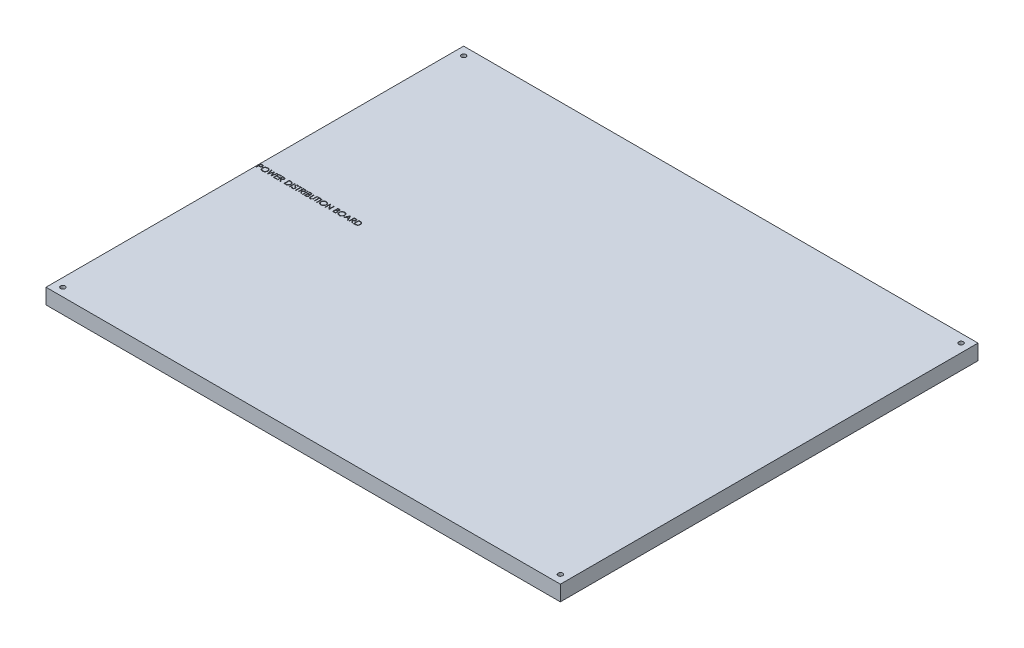
SolidWorks part; units mm, degrees
ref_plane "Front Plane" through (0, 0, 0) normal (0, 0, 1) x (1, 0, 0)
ref_plane "Top Plane" through (0, 0, 0) normal (0, 1, 0) x (1, 0, 0)
ref_plane "Right Plane" through (0, 0, 0) normal (1, 0, 0) x (0, 0, -1)
sketch "Sketch1" plane through (0, 0, 0) normal (0, 1, 0) x (1, 0, 0)
  line L1 (0, 0) -> (335, 0)
  line L2 (0, 0) -> (0, 272)
  line L3 (0, 272) -> (335, 272)
  line L4 (335, 0) -> (335, 272)
  circle A0 centre (5.5, 5.5) radius 1.5
  circle A1 centre (5.5, 266.5) radius 1.5
  circle A2 centre (329.5, 266.5) radius 1.5
  circle A3 centre (329.5, 5.5) radius 1.5
  dimension "D2" = 3
  dimension "D3" = 3
  dimension "D4" = 3
  dimension "D5" = 3
  dimension "D1" = 272
  dimension "D6" = 5.5
  dimension "D7" = 5.5
  dimension "D8" = 5.5
  dimension "D9" = 5.5
  dimension "D10" = 5.5
  dimension "D11" = 5.5
  dimension "D12" = 5.5
  dimension "D13" = 5.5
  dimension "D14" = 335
extrude "Boss-Extrude1" add sketch "Sketch1" along normal blind 10
sketch "Sketch2" plane through (0, 10, 0) normal (0, 1, 0) x (1, 0, 0)
  line L0 (0, 136) -> (335, 136) construction
  line L1 (0, 272) -> (0, 0) construction
  line L2 (335, 0) -> (335, 272) construction
  text T0 "POWER DISTRIBUTION BOARD"
extrude "Cut-Extrude1" cut sketch "Sketch2" against normal through all
